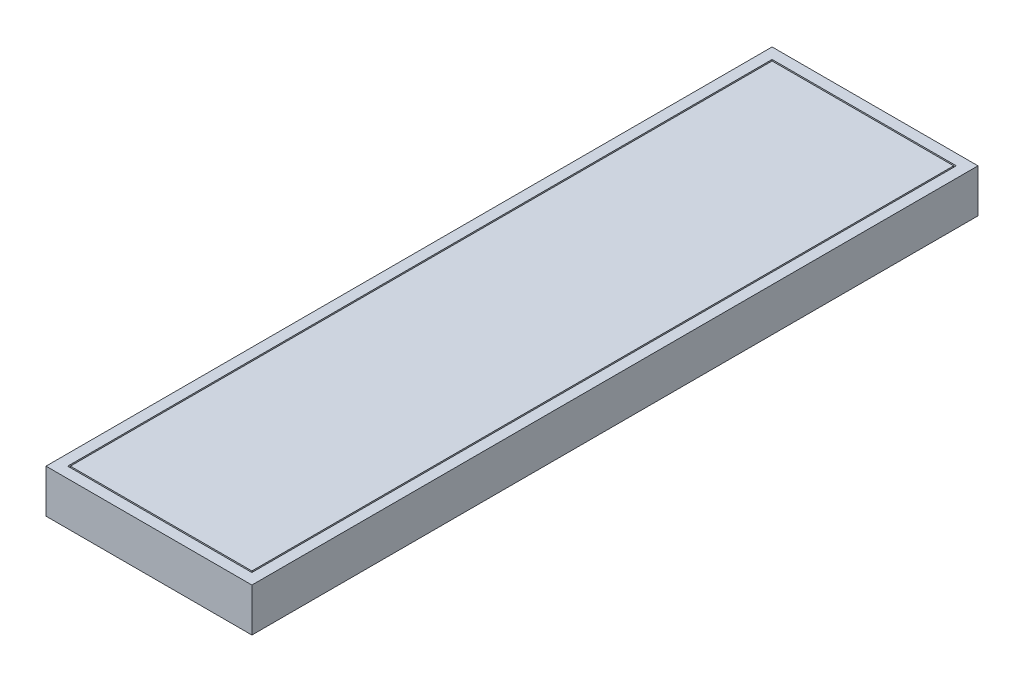
SolidWorks part; units mm, degrees
ref_plane "Front Plane" through (0, 0, 0) normal (0, 0, 1) x (1, 0, 0)
ref_plane "Top Plane" through (0, 0, 0) normal (0, 1, 0) x (1, 0, 0)
ref_plane "Right Plane" through (0, 0, 0) normal (1, 0, 0) x (0, 0, -1)
ref_plane "Plane1" through (0, -60, 0) normal (0, -1, 0) x (1, 0, 0)
sketch "Sketch1" plane through (0, -60, 0) normal (0, -1, 0) x (1, 0, 0)
  line L0 (-190, 0) -> (190, 0)
  line L1 (190, 0) -> (190, 1340)
  line L2 (190, 1340) -> (-190, 1340)
  line L3 (-190, 1340) -> (-190, 0)
  dimension "D1" = 1340
  dimension "D2" = 190
  dimension "D3" = 380
extrude "Boss-Extrude1" add sketch "Sketch1" against normal blind 80
sketch "Sketch2" plane through (0, 20, 0) normal (0, 1, 0) x (-1, 0, 0)
  line L0 (170, 1320) -> (-170, 1320)
  line L1 (-170, 1320) -> (-170, 20)
  line L2 (-170, 20) -> (170, 20)
  line L3 (170, 20) -> (170, 1320)
  dimension "D1" = 20
  dimension "D2" = 1300
  dimension "D3" = 170
  dimension "D4" = 340
extrude "Cut-Extrude1" cut sketch "Sketch2" against normal blind 11
sketch "Sketch3" plane through (0, 9, 0) normal (0, 1, 0) x (-1, 0, 0)
  line L0 (167.5, 1317.5) -> (167.5, 22.5)
  line L1 (167.5, 22.5) -> (-167.5, 22.5)
  line L2 (-167.5, 22.5) -> (-167.5, 1317.5)
  line L3 (-167.5, 1317.5) -> (167.5, 1317.5)
  line L4 (-170, 20) -> (170, 20) construction
  line L5 (170, 20) -> (170, 1320) construction
  dimension "D1" = 2.5
  dimension "D2" = 1295
  dimension "D3" = 2.5
  dimension "D4" = 335
extrude "Boss-Extrude2" add sketch "Sketch3" along normal blind 11
